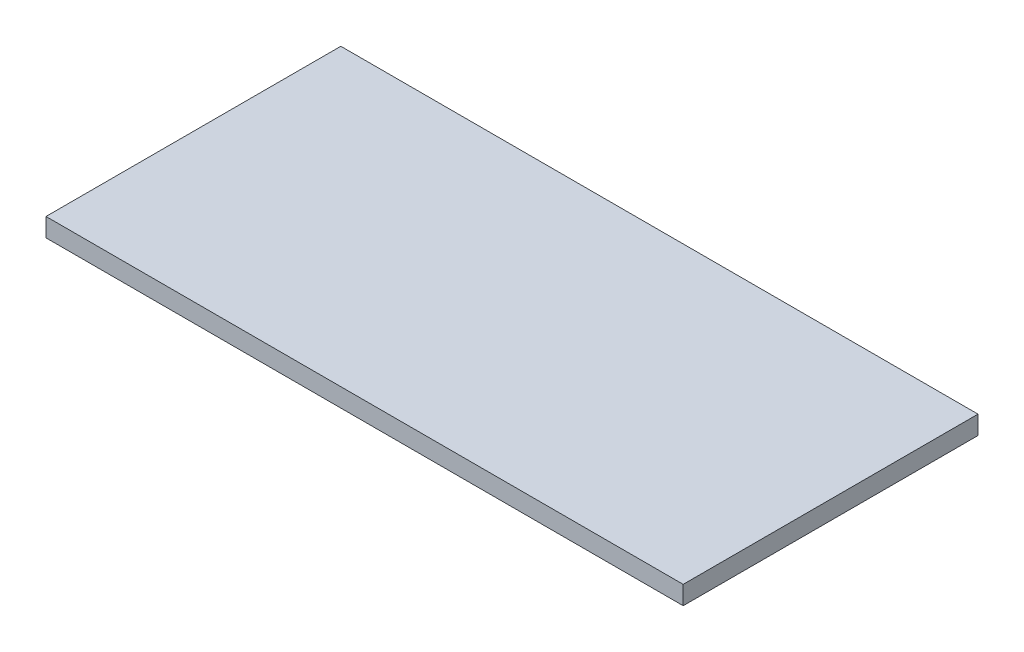
SolidWorks part; units mm, degrees
ref_plane "Front" through (0, 0, 0) normal (0, 0, 1) x (1, 0, 0)
ref_plane "Top" through (0, 0, 0) normal (0, 1, 0) x (1, 0, 0)
ref_plane "Right" through (0, 0, 0) normal (1, 0, 0) x (0, 0, -1)
sketch "草图1" plane through (0, 0, 0) normal (0, 0, 1) x (1, 0, 0)
  line L1 (0, 0) -> (134, 0)
  line L2 (0, 0) -> (0, 3.9)
  line L3 (0, 3.9) -> (134, 3.9)
  line L4 (134, 0) -> (134, 3.9)
  dimension "D1" = 134
  dimension "D2" = 3.9
extrude "凸台-拉伸1" add sketch "草图1" along normal blind 62
